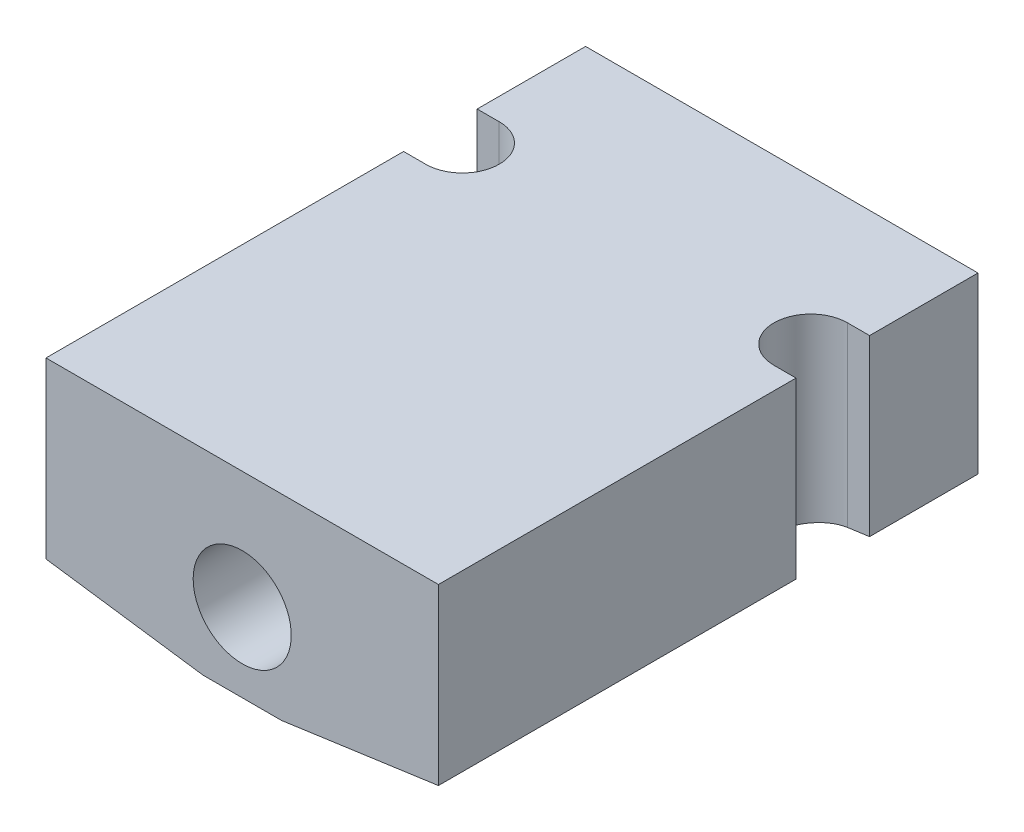
SolidWorks part; units mm, degrees
ref_plane "Front Plane" through (0, 0, 0) normal (0, 0, 1) x (1, 0, 0)
ref_plane "Top Plane" through (0, 0, 0) normal (0, 1, 0) x (1, 0, 0)
ref_plane "Right Plane" through (0, 0, 0) normal (1, 0, 0) x (0, 0, -1)
sketch "Sketch1" plane through (0, 0, 0) normal (0, 0, 1) x (1, 0, 0)
  line L0 (-12.7, -6.35) -> (12.7, -6.35)
  line L1 (-12.7, -6.35) -> (-12.7, 6.35)
  line L2 (12.7, -6.35) -> (12.7, 6.35)
  line L3 (-12.7, 6.35) -> (12.7, 6.35)
  line L4 (-12.7, -6.35) -> (12.7, 6.35) construction
  line L5 (12.7, -6.35) -> (-12.7, 6.35) construction
  point P1 (0, 0)
extrude "Extrude1" add sketch "Sketch1" along normal blind 34.925
sketch "Sketch8" plane through (0, 0, 0) normal (0, 0, -1) x (-1, 0, 0)
  line L0 (0, -6.35) -> (0, -1.27) construction
  line L1 (12.7, -6.35) -> (-12.7, -6.35) construction
chamfer "Chamfer1" distance 10.16 angle 8 2 edges at (-12.7, -6.35, 17.4625) (12.7, -6.35, 17.4625)
hole_wizard "1/4 (0.25) Diameter Hole1" positions "Sketch3" profile "Sketch4" hole size "1/4" standard "Ansi Inch" end condition through all
sketch "Sketch3" plane through (0, 0, 0) normal (0, 0, -1) x (-1, 0, 0)
  line L0 (0, -6.35) -> (0, 6.35) construction
  line L1 (2.54, -6.35) -> (-2.54, -6.35) construction
  line L2 (-12.7, 6.35) -> (12.7, 6.35) construction
  point P15 (0, -1.27)
sketch "Sketch4" plane through (0, -1.27, 0) normal (1, 0, 0) x (0, 1, 0)
  line L0 (0, 0) -> (0, 34.925)
  line L1 (0, 34.925) -> (3.175, 34.925)
  line L2 (3.175, 34.925) -> (3.175, 0)
  line L5 (3.175, 0) -> (0, 0)
  line L11 (0, -6.35) -> (0, 107.95) construction
  dimension "Thru Hole Dia." = 6.35
  dimension "Thru Hole Depth" = 34.925
sketch "Sketch5" plane through (0, 6.35, 0) normal (0, 1, 0) x (1, 0, 0)
  line L0 (-12.7, -9.398) -> (-11.2713, -9.398) construction
  line L1 (-12.7, -34.925) -> (-12.7, 0) construction
  line L2 (-11.2713, -9.398) -> (-11.2713, 0) construction
  line L3 (12.7, 0) -> (-12.7, 0) construction
  line L7 (-11.2713, -11.7792) -> (-12.7, -11.7792)
  line L8 (-12.7, -11.7792) -> (-12.7, -7.0168)
  line L9 (-12.7, -7.0168) -> (-11.2713, -7.0168)
  arc A0 (-11.2713, -11.7792) -> (-11.2713, -7.0168) centre (-11.2713, -9.398) ccw
extrude "Extrude2" cut sketch "Sketch5" against normal through all
mirror "Mirror1" about plane through (0, 0, 0) normal (1, 0, 0) of "Extrude2"
